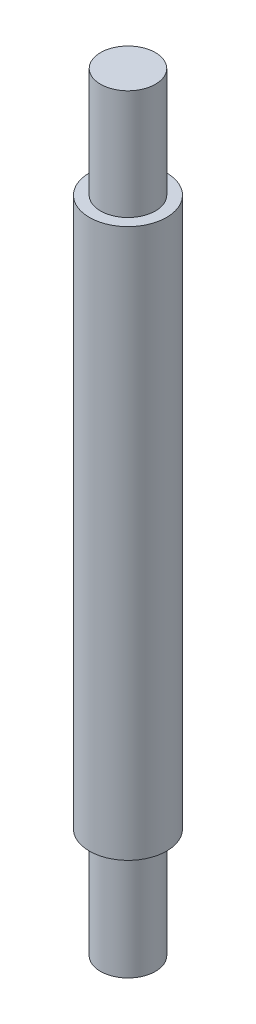
SolidWorks part; units mm, degrees
ref_plane "Front Plane" through (0, 0, 0) normal (0, 0, 1) x (1, 0, 0)
ref_plane "Top Plane" through (0, 0, 0) normal (0, 1, 0) x (1, 0, 0)
ref_plane "Right Plane" through (0, 0, 0) normal (1, 0, 0) x (0, 0, -1)
sketch "Sketch1" plane through (0, 0, 0) normal (0, 1, 0) x (1, 0, 0)
  circle A0 centre (0, 0) radius 3.515
  dimension "D1" = 7.03
extrude "Boss-Extrude1" add sketch "Sketch1" along normal blind 50
sketch "Sketch2" plane through (0, 0, 0) normal (0, 1, 0) x (1, 0, 0)
  circle A0 centre (0, 0) radius 2.5
  dimension "D1" = 5
extrude "Boss-Extrude2" add sketch "Sketch2" against normal blind 10
sketch "Sketch3" plane through (0, 0, 0) normal (0, 1, 0) x (1, 0, 0)
  circle A0 centre (0, 0) radius 2.5
  dimension "D1" = 5
extrude "Boss-Extrude5" add sketch "Sketch3" along normal blind 60
sketch "Sketch6" plane through (0, 0, 0) normal (1, 0, 0) x (0, 0, -1)
  line L0 (0, 60) -> (0, -10) construction
  line L1 (2.5, 60) -> (-2.5, 60) construction
  line L2 (-2.5, -10) -> (2.5, -10) construction
